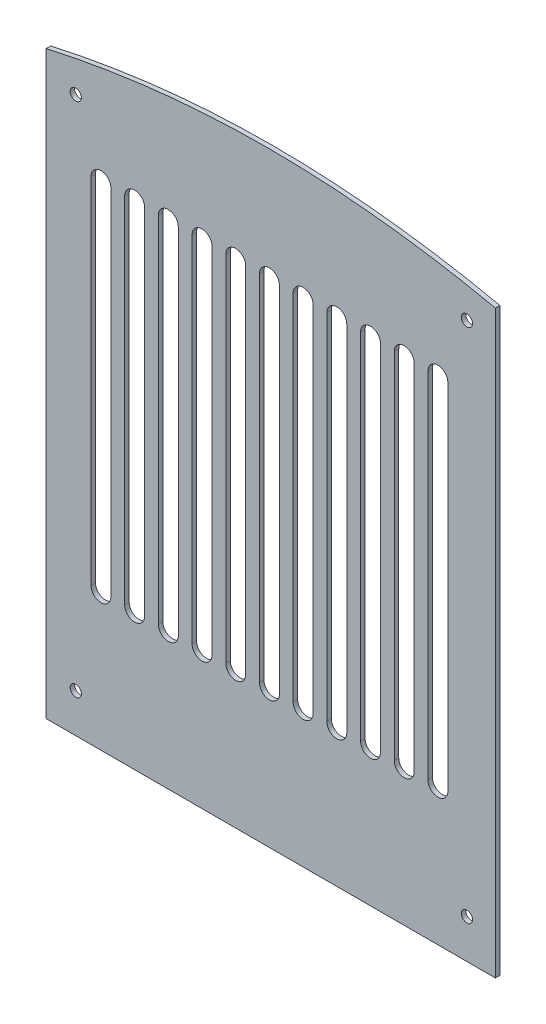
SolidWorks part; units mm, degrees
ref_plane "Front Plane" through (0, 0, 0) normal (0, 0, 1) x (1, 0, 0)
ref_plane "Top Plane" through (0, 0, 0) normal (0, 1, 0) x (1, 0, 0)
ref_plane "Right Plane" through (0, 0, 0) normal (1, 0, 0) x (0, 0, -1)
sketch "Sketch1" plane through (0, 0, 0) normal (0, 0, 1) x (1, 0, 0)
  line L0 (79.9897, 0) -> (-120.0103, 0)
  line L1 (-120.0103, 0) -> (-120.0103, 258.3)
  line L3 (79.9897, 258.3) -> (79.9897, 0)
  line L4 (-95.6044, 219.0311) -> (-95.6044, 61.3452) construction
  line L5 (-91.175, 219.0311) -> (-91.175, 61.3452)
  line L6 (-100.0338, 219.0311) -> (-100.0338, 61.3452)
  line L7 (-80.6044, 219.0311) -> (-80.6044, 61.3452) construction
  line L8 (-76.175, 219.0311) -> (-76.175, 61.3452)
  line L9 (-85.0338, 219.0311) -> (-85.0338, 61.3452)
  line L10 (-65.6044, 219.0311) -> (-65.6044, 61.3452) construction
  line L11 (-61.175, 219.0311) -> (-61.175, 61.3452)
  line L12 (-70.0338, 219.0311) -> (-70.0338, 61.3452)
  line L13 (-50.6044, 219.0311) -> (-50.6044, 61.3452) construction
  line L14 (-46.175, 219.0311) -> (-46.175, 61.3452)
  line L15 (-55.0338, 219.0311) -> (-55.0338, 61.3452)
  line L16 (-35.6044, 219.0311) -> (-35.6044, 61.3452) construction
  line L17 (-31.175, 219.0311) -> (-31.175, 61.3452)
  line L18 (-40.0338, 219.0311) -> (-40.0338, 61.3452)
  line L19 (-20.6044, 219.0311) -> (-20.6044, 61.3452) construction
  line L20 (-16.175, 219.0311) -> (-16.175, 61.3452)
  line L21 (-25.0338, 219.0311) -> (-25.0338, 61.3452)
  line L22 (-5.6044, 219.0311) -> (-5.6044, 61.3452) construction
  line L23 (-1.175, 219.0311) -> (-1.175, 61.3452)
  line L24 (-10.0338, 219.0311) -> (-10.0338, 61.3452)
  line L25 (9.3956, 219.0311) -> (9.3956, 61.3452) construction
  line L26 (13.825, 219.0311) -> (13.825, 61.3452)
  line L27 (4.9662, 219.0311) -> (4.9662, 61.3452)
  line L28 (24.3956, 219.0311) -> (24.3956, 61.3452) construction
  line L29 (28.825, 219.0311) -> (28.825, 61.3452)
  line L30 (19.9662, 219.0311) -> (19.9662, 61.3452)
  line L31 (39.3956, 219.0311) -> (39.3956, 61.3452) construction
  line L32 (43.825, 219.0311) -> (43.825, 61.3452)
  line L33 (34.9662, 219.0311) -> (34.9662, 61.3452)
  line L34 (54.3956, 219.0311) -> (54.3956, 61.3452) construction
  line L35 (58.825, 219.0311) -> (58.825, 61.3452)
  line L36 (49.9662, 219.0311) -> (49.9662, 61.3452)
  arc A0 (-91.175, 219.0311) -> (-100.0338, 219.0311) centre (-95.6044, 219.0311) ccw
  arc A1 (-100.0338, 61.3452) -> (-91.175, 61.3452) centre (-95.6044, 61.3452) ccw
  arc A2 (-76.175, 219.0311) -> (-85.0338, 219.0311) centre (-80.6044, 219.0311) ccw
  arc A3 (-85.0338, 61.3452) -> (-76.175, 61.3452) centre (-80.6044, 61.3452) ccw
  arc A4 (-61.175, 219.0311) -> (-70.0338, 219.0311) centre (-65.6044, 219.0311) ccw
  arc A5 (-70.0338, 61.3452) -> (-61.175, 61.3452) centre (-65.6044, 61.3452) ccw
  arc A6 (-46.175, 219.0311) -> (-55.0338, 219.0311) centre (-50.6044, 219.0311) ccw
  arc A7 (-55.0338, 61.3452) -> (-46.175, 61.3452) centre (-50.6044, 61.3452) ccw
  arc A8 (-31.175, 219.0311) -> (-40.0338, 219.0311) centre (-35.6044, 219.0311) ccw
  arc A9 (-40.0338, 61.3452) -> (-31.175, 61.3452) centre (-35.6044, 61.3452) ccw
  arc A10 (-16.175, 219.0311) -> (-25.0338, 219.0311) centre (-20.6044, 219.0311) ccw
  arc A11 (-25.0338, 61.3452) -> (-16.175, 61.3452) centre (-20.6044, 61.3452) ccw
  arc A12 (-1.175, 219.0311) -> (-10.0338, 219.0311) centre (-5.6044, 219.0311) ccw
  arc A13 (-10.0338, 61.3452) -> (-1.175, 61.3452) centre (-5.6044, 61.3452) ccw
  arc A14 (13.825, 219.0311) -> (4.9662, 219.0311) centre (9.3956, 219.0311) ccw
  arc A15 (4.9662, 61.3452) -> (13.825, 61.3452) centre (9.3956, 61.3452) ccw
  arc A16 (28.825, 219.0311) -> (19.9662, 219.0311) centre (24.3956, 219.0311) ccw
  arc A17 (19.9662, 61.3452) -> (28.825, 61.3452) centre (24.3956, 61.3452) ccw
  arc A18 (43.825, 219.0311) -> (34.9662, 219.0311) centre (39.3956, 219.0311) ccw
  arc A19 (34.9662, 61.3452) -> (43.825, 61.3452) centre (39.3956, 61.3452) ccw
  arc A20 (58.825, 219.0311) -> (49.9662, 219.0311) centre (54.3956, 219.0311) ccw
  arc A21 (49.9662, 61.3452) -> (58.825, 61.3452) centre (54.3956, 61.3452) ccw
  circle A22 centre (-106.8037, 247.1774) radius 2.5
  circle A23 centre (67.3225, 247.1774) radius 2.5
  circle A24 centre (67.3225, 17.3422) radius 2.5
  circle A25 centre (-106.8037, 17.3422) radius 2.5
  spline S0 degree 2 poles (-120.0103, 258.3) (-22.4945, 280.451) (79.9897, 258.3) knots 0 0 0 1 1 1
  point P7 (-95.6044, 140.1882)
  point P15 (-80.6044, 140.1882)
  point P22 (-65.6044, 140.1882)
  point P29 (-50.6044, 140.1882)
  point P36 (-35.6044, 140.1882)
  point P43 (-20.6044, 140.1882)
  point P50 (-5.6044, 140.1882)
  point P57 (9.3956, 140.1882)
  point P64 (24.3956, 140.1882)
  point P71 (39.3956, 140.1882)
  point P78 (54.3956, 140.1882)
  dimension "D1" = 258.3
  dimension "D2" = 200
  dimension "D3" = 11
extrude "Boss-Extrude1" add sketch "Sketch1" along normal blind 2
